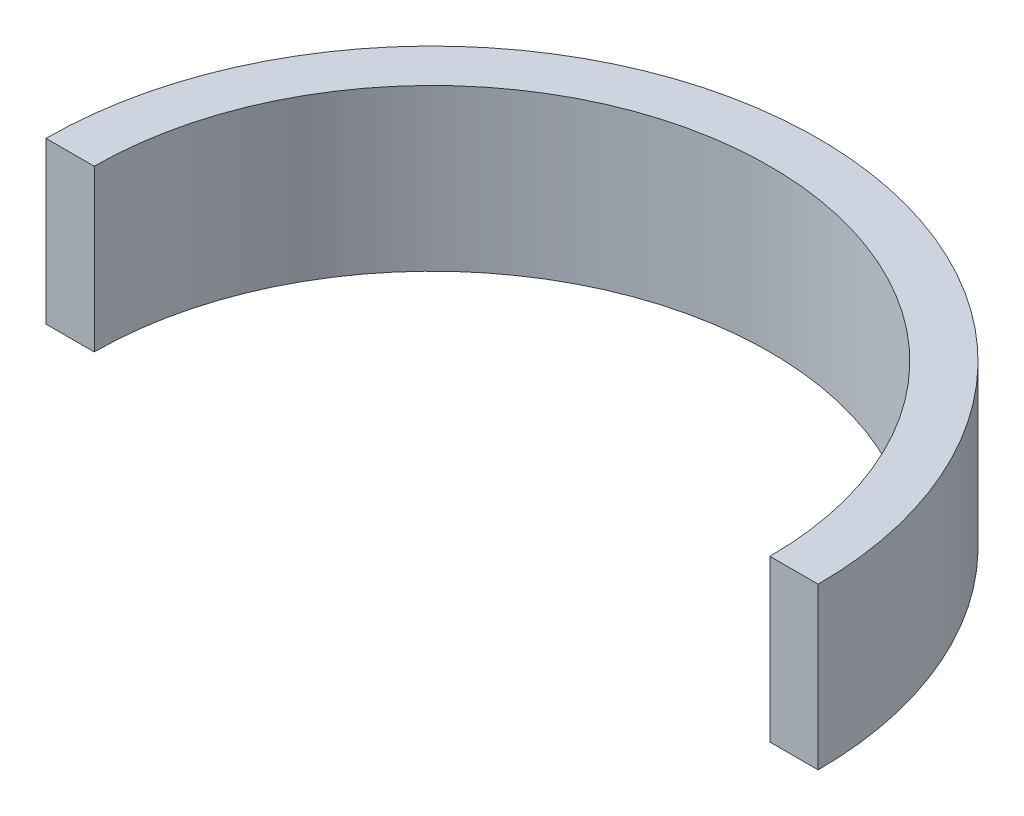
SolidWorks part; units mm, degrees
ref_plane "Front" through (0, 0, 0) normal (0, 0, 1) x (1, 0, 0)
ref_plane "Top" through (0, 0, 0) normal (0, 1, 0) x (1, 0, 0)
ref_plane "Right" through (0, 0, 0) normal (1, 0, 0) x (0, 0, -1)
sketch "草图1" plane through (0, 0, 0) normal (0, 1, 0) x (1, 0, 0)
  line L0 (42, 0) -> (48, 0)
  line L1 (-48, 0) -> (-42, 0)
  arc A0 (48, 0) -> (-48, 0) centre (0, 0) ccw
  arc A1 (42, 0) -> (-42, 0) centre (0, 0) ccw
extrude "凸台-拉伸1" add sketch "草图1" along normal blind 20
